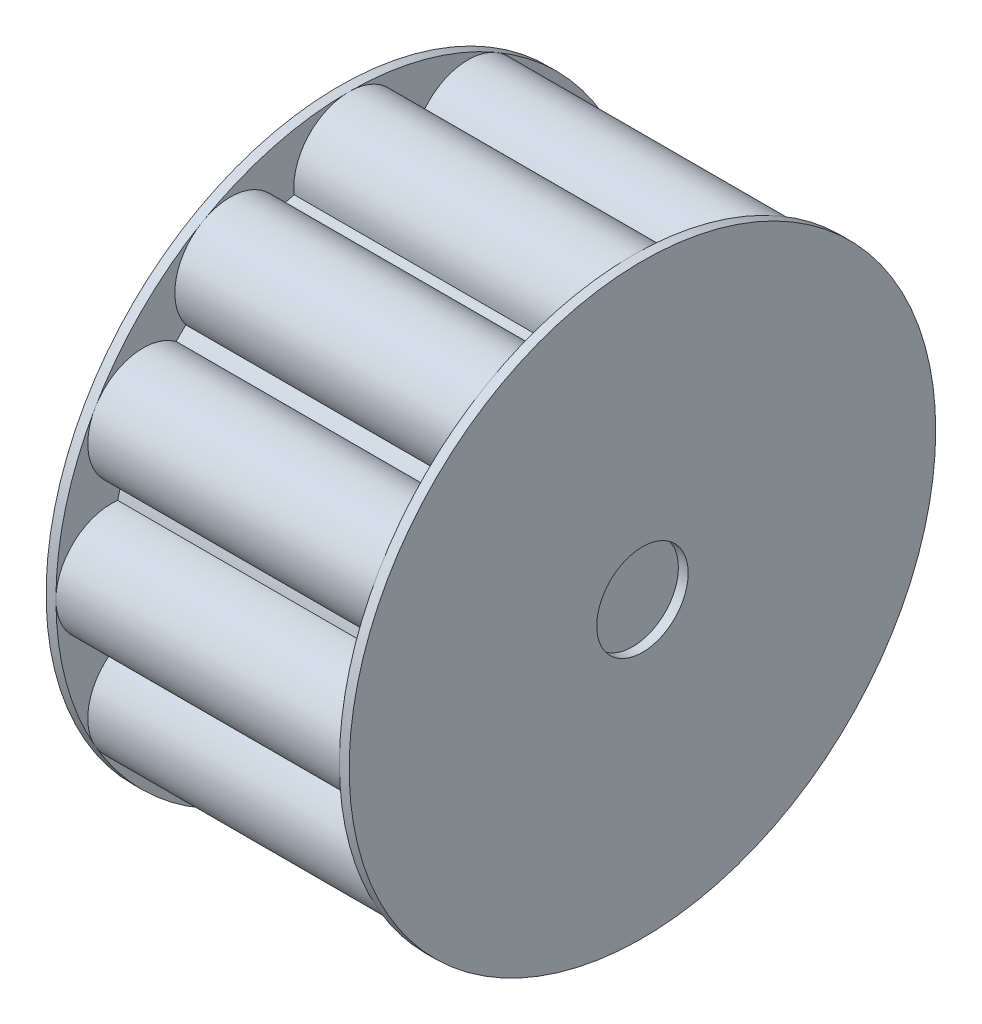
SolidWorks part; units mm, degrees
ref_plane "Front Plane" through (0, 0, 0) normal (0, 0, 1) x (1, 0, 0)
ref_plane "Top Plane" through (0, 0, 0) normal (0, 1, 0) x (1, 0, 0)
ref_plane "Right Plane" through (0, 0, 0) normal (1, 0, 0) x (0, 0, -1)
sketch "Sketch1" plane through (0, 0, 0) normal (1, 0, 0) x (0, 0, -1)
  circle A0 centre (0, 0) radius 30
  dimension "D1" = 60
extrude "Boss-Extrude1" add sketch "Sketch1" along normal blind 1
sketch "Sketch2" plane through (1, 0, 0) normal (1, 0, 0) x (0, 0, -1)
  circle A0 centre (0, 0) radius 24.3359
extrude "Boss-Extrude2" add sketch "Sketch2" along normal blind 29
sketch "Sketch3" plane through (30, 0, 0) normal (1, 0, 0) x (0, 0, -1)
  circle A0 centre (0, 24.3359) radius 5.6641
  circle A1 centre (0, 0) radius 24.3359 construction
  circle A2 centre (0, 0) radius 24.3359 construction
  circle A3 centre (12.1679, 21.0755) radius 5.6641
  circle A4 centre (21.0755, 12.1679) radius 5.6641
  circle A5 centre (24.3359, 0) radius 5.6641
  circle A6 centre (21.0755, -12.1679) radius 5.6641
  circle A7 centre (12.1679, -21.0755) radius 5.6641
  circle A8 centre (0, -24.3359) radius 5.6641
  circle A9 centre (-12.1679, -21.0755) radius 5.6641
  circle A10 centre (-21.0755, -12.1679) radius 5.6641
  circle A11 centre (-24.3359, 0) radius 5.6641
  circle A12 centre (-21.0755, 12.1679) radius 5.6641
  circle A13 centre (-12.1679, 21.0755) radius 5.6641
  dimension "D1" = 12
extrude "Boss-Extrude3" add sketch "Sketch3" against normal blind 29
sketch "Sketch4" plane through (30, 0, 0) normal (1, 0, 0) x (0, 0, -1)
  circle A0 centre (0, 0) radius 30
extrude "Boss-Extrude4" add sketch "Sketch4" along normal blind 1
sketch "Sketch5" plane through (0, 0, 0) normal (-1, 0, 0) x (0, 0, 1)
  circle A0 centre (0, 0) radius 4.6815
extrude "Cut-Extrude1" cut sketch "Sketch5" against normal blind 1
sketch "Sketch6" plane through (31, 0, 0) normal (1, 0, 0) x (0, 0, -1)
  circle A0 centre (0, 0) radius 4.6787
extrude "Cut-Extrude2" cut sketch "Sketch6" against normal blind 1
